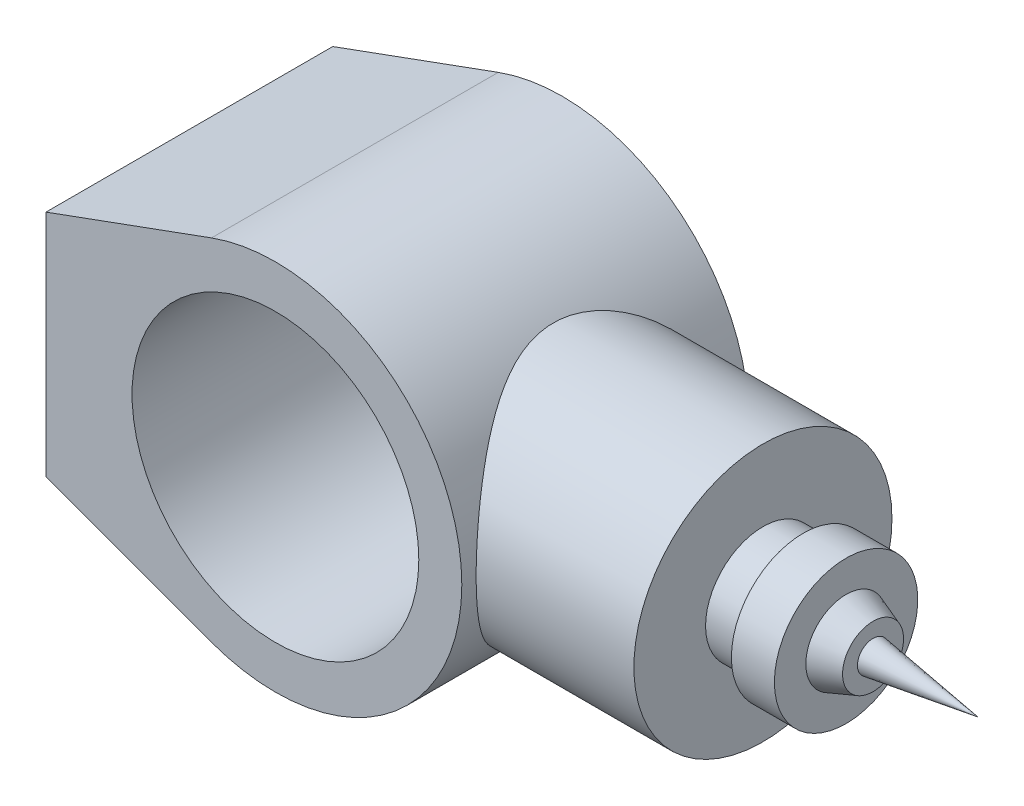
SolidWorks part; units mm, degrees
ref_plane "Ön Düzlem" through (0, 0, 0) normal (0, 0, 1) x (1, 0, 0)
ref_plane "Üst Düzlem" through (0, 0, 0) normal (0, 1, 0) x (1, 0, 0)
ref_plane "Sağ Düzlem" through (0, 0, 0) normal (1, 0, 0) x (0, 0, -1)
sketch "Çizim1" plane through (0, 0, 0) normal (0, 0, 1) x (1, 0, 0)
  line L0 (-80, -40) -> (-80, 40)
  line L1 (-80, 40) -> (-22.2817, 61.0617)
  line L2 (-80, -40) -> (-22.2817, -61.0617)
  arc A0 (-22.2817, -61.0617) -> (-22.2817, 61.0617) centre (0, 0) ccw
  circle A1 centre (0, 0) radius 50
  point P7 (-80, 0)
  dimension "D1" = 100
  dimension "D2" = 130
  dimension "D3" = 80
  dimension "D4" = 80
extrude "Yükseklik-Ekstrüzyon1" add sketch "Çizim1" along normal blind 100
ref_plane "Düzlem1" through (120, 0, 0) normal (1, 0, 0) x (0, 0, -1)
sketch "Çizim3" plane through (120, 0, 0) normal (1, 0, 0) x (0, 0, -1)
  line L0 (-50, 65) -> (-50, -65) construction
  line L1 (0, 65) -> (-100, 65) construction
  line L2 (-100, -65) -> (0, -65) construction
  circle A0 centre (-50, 0) radius 45
  dimension "D1" = 90
extrude "Yükseklik-Ekstrüzyon2" add sketch "Çizim3" against normal up to next
ref_plane "Düzlem2" through (0, 0, 50) normal (0, 0, 1) x (1, 0, 0)
sketch "Çizim6" plane through (0, 0, 50) normal (0, 0, 1) x (1, 0, 0)
  line L0 (-133.943, 0) -> (223.9279, 0) construction
  line L1 (120, 0) -> (120, -20)
  line L2 (120, -20) -> (134, -20)
  line L3 (134, -20) -> (134, -25)
  line L4 (134, -25) -> (149, -25)
  line L5 (149, -25) -> (149, -14.0331)
  line L6 (149, -14.0331) -> (158.4039, -10.632)
  line L7 (158.4039, -10.632) -> (158.4039, -5.4519)
  line L8 (158.4039, -5.4519) -> (195, 0)
  line L9 (195, 0) -> (120, 0)
  line L10 (120, -45) -> (120, 45) construction
  dimension "D1" = 15
  dimension "D2" = 10
  dimension "D3" = 37
  dimension "D4" = 75
revolve "Döndür1" add sketch "Çizim6" angle 360 about L0
